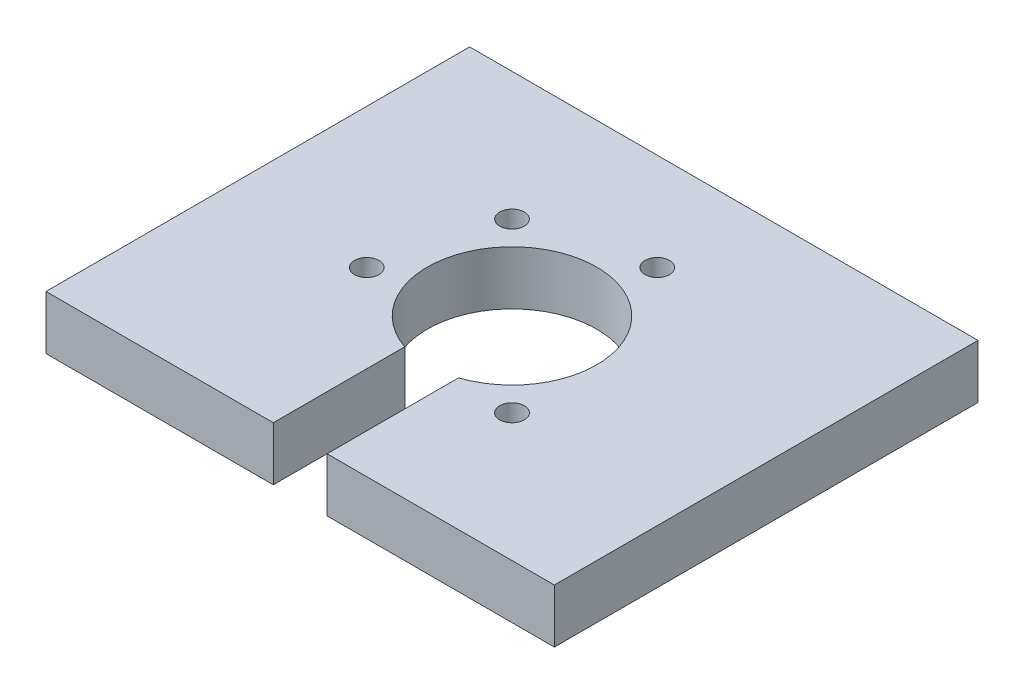
SolidWorks part; units mm, degrees
ref_plane "Front Plane" through (0, 0, 0) normal (0, 0, 1) x (1, 0, 0)
ref_plane "Top Plane" through (0, 0, 0) normal (0, 1, 0) x (1, 0, 0)
ref_plane "Right Plane" through (0, 0, 0) normal (1, 0, 0) x (0, 0, -1)
sketch "Sketch1" plane through (0, 0, 0) normal (0, 1, 0) x (1, 0, 0)
  line L1 (0, 0) -> (-60, 0)
  line L2 (0, 0) -> (0, -50)
  line L3 (0, -50) -> (-60, -50)
  line L4 (-60, 0) -> (-60, -50)
  dimension "D1" = 60
  dimension "D2" = 50
extrude "Boss-Extrude1" add sketch "Sketch1" along normal blind 6.35
sketch "Sketch2" plane through (0, 6.35, 0) normal (0, 1, 0) x (1, 0, 0)
  line L0 (-30, 0) -> (-30, -50) construction
  line L2 (0, 0) -> (-60, 0) construction
  line L4 (-60, -50) -> (0, -50) construction
  line L5 (-60, -25) -> (0, -25) construction
  line L6 (-60, 0) -> (-60, -50) construction
  line L7 (0, -50) -> (0, 0) construction
  line L9 (-26.825, -20) -> (-33.175, -20)
  line L10 (-26.825, -20) -> (-26.825, -50)
  line L11 (-26.825, -50) -> (-33.175, -50)
  line L12 (-33.175, -20) -> (-33.175, -50)
  line L13 (-26.825, -20) -> (-33.175, -50) construction
  line L14 (-26.825, -50) -> (-33.175, -20) construction
  circle A0 centre (-30, -25) radius 19 construction
  circle A1 centre (-30, -25) radius 10
  point P16 (-30, -35)
  line M6 (-60, -50) -> (0, -50)
  dimension "D1" = 38
  dimension "D2" = 20
  dimension "D3" = 6.35
extrude "Cut-Extrude1" cut sketch "Sketch2" against normal blind 6.35 contours L10 A1 L12 L9 | L12 A1 L10 L9 | A1 L12 L10 M6
sketch "Sketch3" plane through (0, 6.35, 0) normal (0, 1, 0) x (1, 0, 0)
  line L0 (-30, -25) -> (-30, 0) construction
  line L1 (0, 0) -> (-60, 0) construction
  line L2 (-30, -25) -> (-39.8995, -15.1005) construction
  line L3 (-30, -25) -> (-26.3765, -11.477) construction
  line L4 (-30, -25) -> (-43.523, -28.6235) construction
  line L5 (-30, -25) -> (-20.1005, -34.8995) construction
  circle A0 centre (-30, -25) radius 14 construction
  point P3 (-26.3765, -11.477)
  point P7 (-39.8995, -15.1005)
  dimension "D1" = 28
  dimension "D2" = 45
  dimension "D3" = 15
  dimension "D4" = 120
  dimension "D5" = 120
hole_wizard "M3.5x0.6 Tapped Hole1" positions "3DSketch1" profile "Sketch4" tap size "M3.5x0.6" standard "ANSI Metric" end condition through all
sketch3d "3DSketch1"
  point P0 (-26.3765, 6.35, 11.477)
  point P3 (-39.8995, 6.35, 15.1005)
  point P6 (-43.523, 6.35, 28.6235)
  point P9 (-20.1005, 6.35, 34.8995)
sketch "Sketch4" plane through (-26.3765, 6.35, 11.477) normal (1, 0, 0) x (0, 0, 1)
  line L0 (0, 0) -> (0, 6.35)
  line L1 (0, 6.35) -> (1.45, 6.35)
  line L2 (1.45, 6.35) -> (1.45, 0)
  line L5 (1.45, 0) -> (0, 0)
  line L11 (0, -6.35) -> (0, 107.95) construction
  dimension "Thru Tap Drill Dia." = 2.9
  dimension "Thru Tap Drill Depth" = 6.35
cosmetic thread "Hole Thread1" parameters "D2"=3.5
cosmetic thread "Hole Thread2" parameters "D2"=3.5
cosmetic thread "Hole Thread3" parameters "D2"=3.5
cosmetic thread "Hole Thread4" parameters "D2"=3.5
sketch "Sketch5" plane through (0, 0, 0) normal (0, 0, -1) x (-1, 0, 0)
  line L0 (0, 3.175) -> (60, 3.175) construction
  line L1 (0, 6.35) -> (0, 0) construction
  line L2 (60, 6.35) -> (60, 0) construction
  point P6 (30, 3.175)
  point P7 (8, 3.175)
  point P8 (52, 3.175)
  dimension "D1" = 22
  dimension "D2" = 22
hole_wizard "M4x0.7 Tapped Hole1" positions "3DSketch2" profile "Sketch7" tap size "M4x0.7" standard "ANSI Metric"
sketch3d "3DSketch2"
  point P0 (-8, 3.175, 0)
  point P3 (-30, 3.175, 0)
  point P6 (-52, 3.175, 0)
sketch "Sketch7" plane through (-8, 3.175, 0) normal (1, 0, 0) x (0, 1, 0)
  line L0 (0, 0) -> (0, 7.3414)
  line L1 (0, 7.3414) -> (1.65, 6.35)
  line L2 (1.65, 6.35) -> (1.65, 0)
  line L5 (1.65, 0) -> (0, 0)
  line L10 (0, 7.3414) -> (-1.65, 6.35) construction
  line L11 (0, -6.35) -> (0, 107.95) construction
  dimension "Tap Drill Dia." = 3.3
  dimension "Tap Drill Depth" = 6.35
  dimension "Drill Angle" = 118
cosmetic thread "Hole Thread5" parameters "D1"=6.35, "D2"=4
cosmetic thread "Hole Thread6" parameters "D1"=6.35, "D2"=4
cosmetic thread "Hole Thread7" parameters "D1"=6.35, "D2"=4
